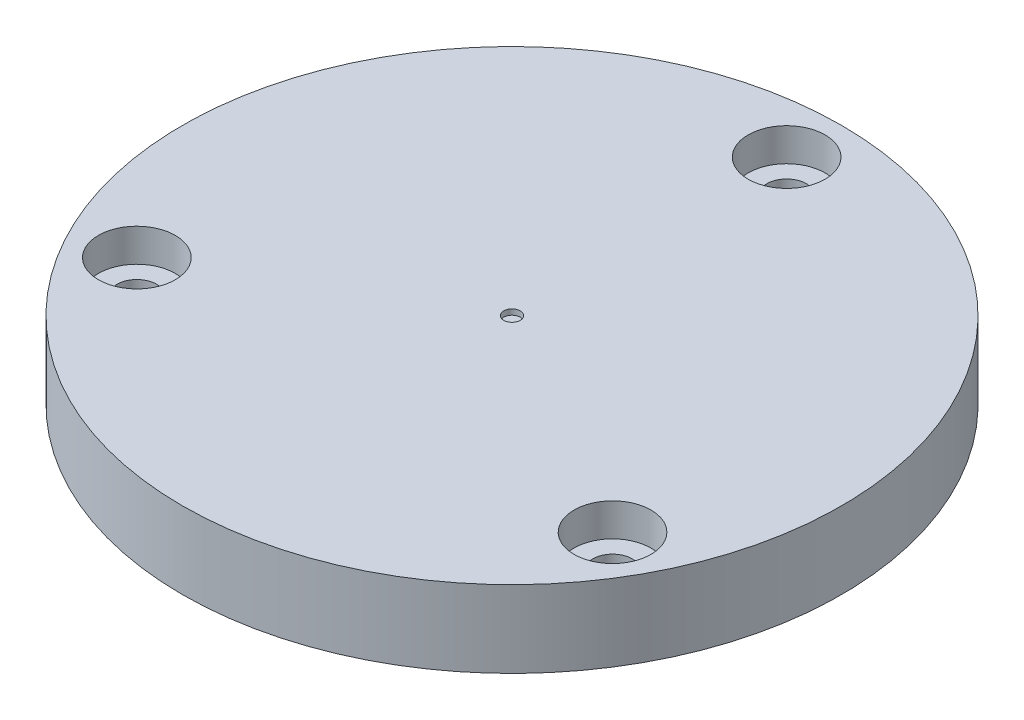
SolidWorks part; units mm, degrees
ref_plane "Front Plane" through (0, 0, 0) normal (0, 0, 1) x (1, 0, 0)
ref_plane "Top Plane" through (0, 0, 0) normal (0, 1, 0) x (1, 0, 0)
ref_plane "Right Plane" through (0, 0, 0) normal (1, 0, 0) x (0, 0, -1)
sketch "Sketch1" plane through (0, 0, 0) normal (0, 1, 0) x (1, 0, 0)
  circle A0 centre (0, 0) radius 30
  circle A2 centre (0, 25) radius 1.8
  circle A3 centre (21.6506, -12.5) radius 1.8
  circle A4 centre (-21.6506, -12.5) radius 1.8
  point P3 (0, 0)
  point P7 (-15.5572, 2.3814)
  point P12 (0, 0)
  point P19 (0, 0)
  dimension "D1" = 60
  dimension "D3" = 3.6
  dimension "D4" = 25
  dimension "D5" = 3
extrude "Boss-Extrude1" add sketch "Sketch1" along normal blind 7
sketch "Sketch2" plane through (0, 7, 0) normal (0, 1, 0) x (1, 0, 0)
  circle A1 centre (0, 25) radius 3.5
  circle A2 centre (21.6506, -12.5) radius 3.5
  circle A3 centre (-21.6506, -12.5) radius 3.5
  point P2 (-18.9194, -4.7986)
  point P3 (0, 0)
  point P8 (0, 0)
  dimension "D1" = 7
  dimension "D2" = 3
extrude "Cut-Extrude1" cut sketch "Sketch2" against normal blind 3
sketch "Sketch3" plane through (0, 7, 0) normal (0, 1, 0) x (1, 0, 0)
  circle A0 centre (0, 0) radius 0.75
  dimension "D1" = 1.5
extrude "Cut-Extrude2" cut sketch "Sketch3" against normal blind 0.5
